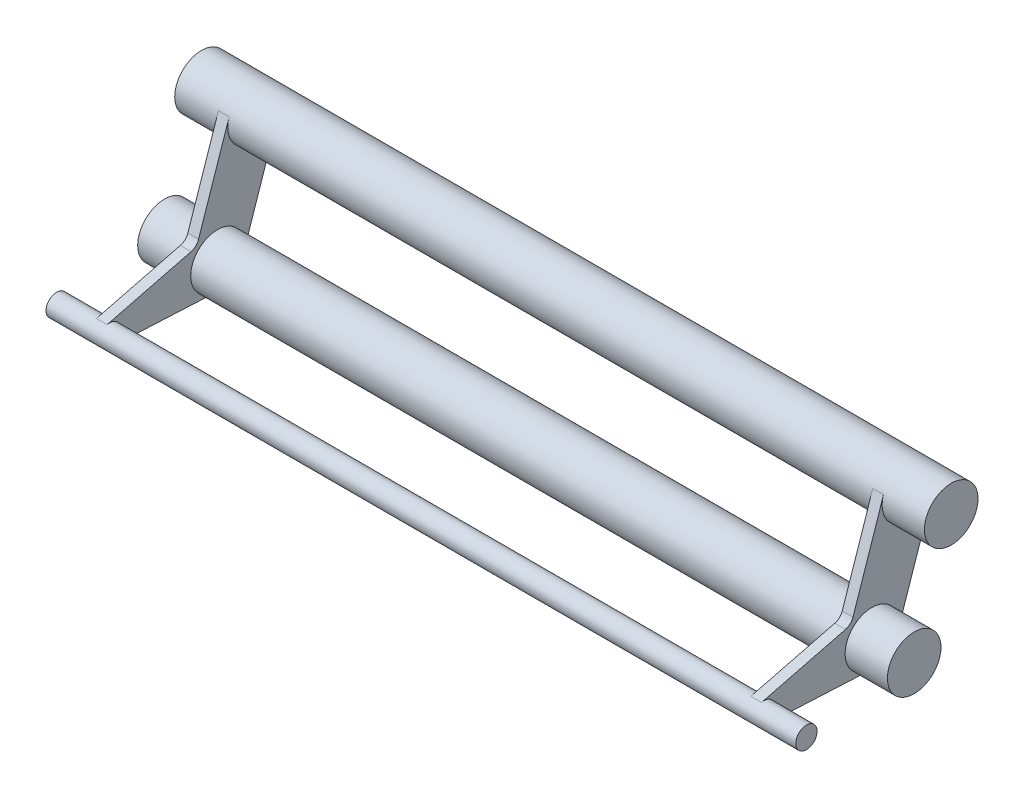
SolidWorks part; units mm, degrees
ref_plane "Alzado" through (0, 0, 0) normal (0, 0, 1) x (1, 0, 0)
ref_plane "Planta" through (0, 0, 0) normal (0, 1, 0) x (1, 0, 0)
ref_plane "Vista lateral" through (0, 0, 0) normal (1, 0, 0) x (0, 0, -1)
sketch "Croquis1" plane through (0, 0, 0) normal (1, 0, 0) x (0, 0, -1)
  line L0 (0, 0) -> (-6.9151, -20.5793) construction
  line L1 (-6.9151, -20.5793) -> (-27.0359, -22.5793) construction
  circle A4 centre (0, 0) radius 5
  circle A5 centre (-6.9151, -20.5793) radius 5
  circle A6 centre (-27.0359, -22.5793) radius 2
  dimension "D1" = 4
  dimension "D2" = 10
  dimension "D3" = 10
  dimension "D4" = 20.22
  dimension "D5" = 21.71
  dimension "D6" = 114.25
extrude "Saliente-Extruir6" add sketch "Croquis1" along normal blind 120.2
sketch "Croquis10" plane through (0, 0, 0) normal (-1, 0, 0) x (0, 0, 1)
  line L0 (-4.7396, -1.5926) -> (2.1755, -22.1719)
  line L1 (4.7396, 1.5926) -> (10.4386, -15.3676)
  line L2 (11.8435, -16.6694) -> (27.5268, -20.6404)
  line L3 (7.1642, -25.573) -> (27.1356, -24.5768)
  circle A0 centre (27.0359, -22.5793) radius 2 construction
  circle A1 centre (0, 0) radius 5
  arc A2 (4.7396, 1.5926) -> (-4.7396, -1.5926) centre (0, 0) ccw
  circle A3 centre (6.9151, -20.5793) radius 5 construction
  arc A4 (27.1356, -24.5768) -> (27.5268, -20.6404) centre (27.0359, -22.5793) ccw
  arc A5 (2.1755, -22.1719) -> (7.1642, -25.573) centre (6.9151, -20.5793) ccw
  arc A6 (11.8435, -16.6694) -> (10.4386, -15.3676) centre (12.3344, -14.7305) cw
  dimension "D2" = 2
  dimension "D1" = 0
extrude "Saliente-Extruir8" add sketch "Croquis10" along normal blind 2
sketch "Croquis11" plane through (120.2, 0, 0) normal (1, 0, 0) x (0, 0, -1)
  line L0 (4.7396, -1.5926) -> (-2.1755, -22.1719) construction
  line L1 (-7.1642, -25.573) -> (-27.1356, -24.5768) construction
  line L2 (-27.5268, -20.6404) -> (-11.8435, -16.6694) construction
  line L3 (-10.4386, -15.3676) -> (-4.7396, 1.5926) construction
  line L4 (4.7396, -1.5926) -> (-2.1755, -22.1719)
  line L5 (-7.1642, -25.573) -> (-27.1356, -24.5768)
  line L6 (-27.5268, -20.6404) -> (-11.8435, -16.6694)
  line L7 (-10.4386, -15.3676) -> (-4.7396, 1.5926)
  circle A0 centre (-6.9151, -20.5793) radius 5 construction
  circle A1 centre (-27.0359, -22.5793) radius 2 construction
  arc A2 (-11.8435, -16.6694) -> (-10.4386, -15.3676) centre (-12.3344, -14.7305) ccw construction
  circle A3 centre (0, 0) radius 5 construction
  arc A4 (-7.1642, -25.573) -> (-2.1755, -22.1719) centre (-6.9151, -20.5793) ccw
  arc A5 (-27.5268, -20.6404) -> (-27.1356, -24.5768) centre (-27.0359, -22.5793) ccw
  arc A6 (-11.8435, -16.6694) -> (-10.4386, -15.3676) centre (-12.3344, -14.7305) ccw
  arc A7 (4.7396, -1.5926) -> (-4.7396, 1.5926) centre (0, 0) ccw
extrude "Saliente-Extruir9" add sketch "Croquis11" along normal blind 2
sketch "Croquis13" plane through (122.2, 0, 0) normal (1, 0, 0) x (0, 0, -1)
  line L4 (-4.7396, 1.5926) -> (-10.4386, -15.3676)
  line L5 (-11.8435, -16.6694) -> (-27.5268, -20.6404)
  line L6 (-27.1356, -24.5768) -> (-7.1642, -25.573)
  line L7 (-2.1755, -22.1719) -> (4.7396, -1.5926)
  line L8 (-4.7396, 1.5926) -> (-10.4386, -15.3676)
  line L9 (-11.8435, -16.6694) -> (-27.5268, -20.6404)
  line L10 (-27.1356, -24.5768) -> (-7.1642, -25.573)
  line L11 (-2.1755, -22.1719) -> (4.7396, -1.5926)
  circle A0 centre (0, 0) radius 5
  circle A1 centre (-6.9151, -20.5793) radius 5
  circle A2 centre (-27.0359, -22.5793) radius 2
  arc A4 (4.7396, -1.5926) -> (-4.7396, 1.5926) centre (0, 0) ccw
  arc A5 (-11.8435, -16.6694) -> (-10.4386, -15.3676) centre (-12.3344, -14.7305) ccw
  arc A6 (-27.5268, -20.6404) -> (-27.1356, -24.5768) centre (-27.0359, -22.5793) ccw
  arc A7 (-7.1642, -25.573) -> (-2.1755, -22.1719) centre (-6.9151, -20.5793) ccw
  arc A8 (4.7396, -1.5926) -> (-4.7396, 1.5926) centre (0, 0) ccw
  arc A9 (-11.8435, -16.6694) -> (-10.4386, -15.3676) centre (-12.3344, -14.7305) ccw
  arc A10 (-27.5268, -20.6404) -> (-27.1356, -24.5768) centre (-27.0359, -22.5793) ccw
  arc A11 (-7.1642, -25.573) -> (-2.1755, -22.1719) centre (-6.9151, -20.5793) ccw
  arc M9 (4.7396, -1.5926) -> (-4.7396, 1.5926) centre (0, 0) ccw
  arc M13 (-27.5268, -20.6404) -> (-27.1356, -24.5768) centre (-27.0359, -22.5793) ccw
  arc M15 (-7.1642, -25.573) -> (-2.1755, -22.1719) centre (-6.9151, -20.5793) ccw
  dimension "D1" = 0
extrude "Saliente-Extruir10" add sketch "Croquis13" along normal blind 7.9 contours A1 M15 | A0 M9 | A2 M13
sketch "Croquis14" plane through (-2, 0, 0) normal (-1, 0, 0) x (0, 0, 1)
  line L4 (10.4386, -15.3676) -> (4.7396, 1.5926)
  line L5 (-4.7396, -1.5926) -> (2.1755, -22.1719)
  line L6 (7.1642, -25.573) -> (27.1356, -24.5768)
  line L7 (27.5268, -20.6404) -> (11.8435, -16.6694)
  line L8 (10.4386, -15.3676) -> (4.7396, 1.5926)
  line L9 (-4.7396, -1.5926) -> (2.1755, -22.1719)
  line L10 (7.1642, -25.573) -> (27.1356, -24.5768)
  line L11 (27.5268, -20.6404) -> (11.8435, -16.6694)
  circle A0 centre (0, 0) radius 5
  circle A1 centre (6.9151, -20.5793) radius 5
  circle A2 centre (27.0359, -22.5793) radius 2
  arc A4 (10.4386, -15.3676) -> (11.8435, -16.6694) centre (12.3344, -14.7305) ccw
  arc A5 (4.7396, 1.5926) -> (-4.7396, -1.5926) centre (0, 0) ccw
  arc A6 (2.1755, -22.1719) -> (7.1642, -25.573) centre (6.9151, -20.5793) ccw
  arc A7 (27.1356, -24.5768) -> (27.5268, -20.6404) centre (27.0359, -22.5793) ccw
  arc A8 (10.4386, -15.3676) -> (11.8435, -16.6694) centre (12.3344, -14.7305) ccw
  arc A9 (4.7396, 1.5926) -> (-4.7396, -1.5926) centre (0, 0) ccw
  arc A10 (2.1755, -22.1719) -> (7.1642, -25.573) centre (6.9151, -20.5793) ccw
  arc A11 (27.1356, -24.5768) -> (27.5268, -20.6404) centre (27.0359, -22.5793) ccw
  arc M11 (4.7396, 1.5926) -> (-4.7396, -1.5926) centre (0, 0) ccw
  arc M13 (2.1755, -22.1719) -> (7.1642, -25.573) centre (6.9151, -20.5793) ccw
  arc M15 (27.1356, -24.5768) -> (27.5268, -20.6404) centre (27.0359, -22.5793) ccw
  dimension "D1" = 0
extrude "Saliente-Extruir11" add sketch "Croquis14" along normal blind 7.9 contours A0 M11 | A1 M13 | A2 M15 | L10 A11 L11 A8 L8 A9 L9 A10
